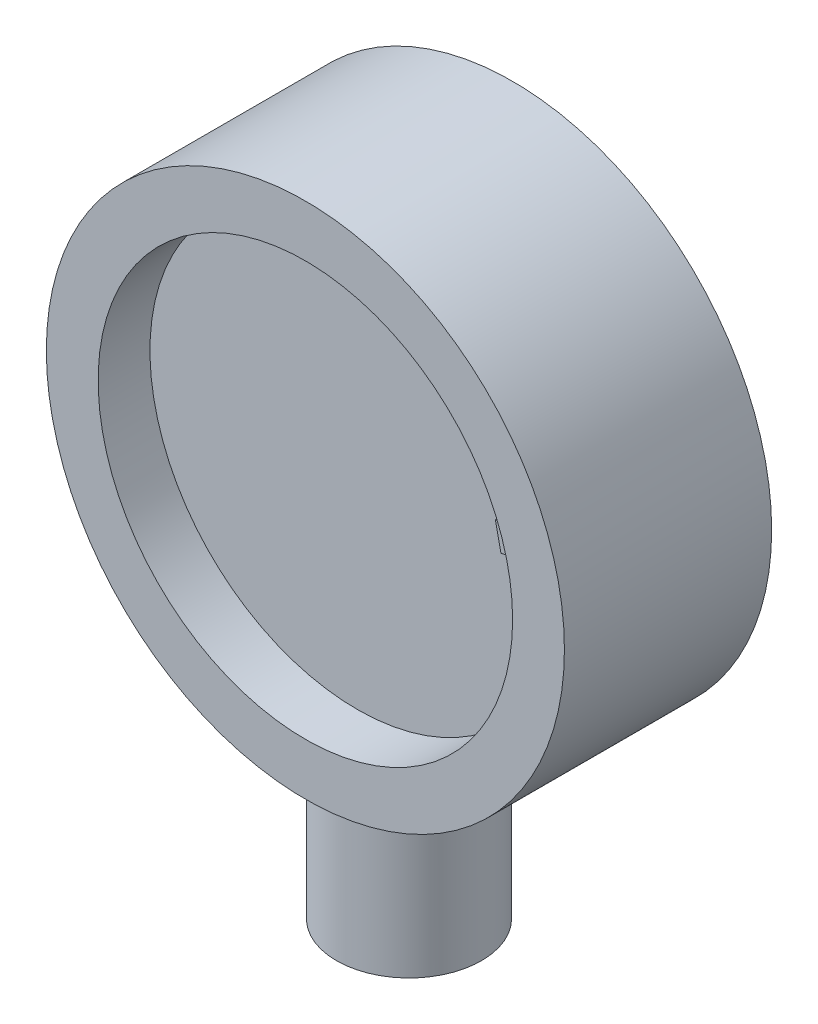
SolidWorks part; units mm, degrees
ref_plane "Спереди" through (0, 0, 0) normal (0, 0, 1) x (1, 0, 0)
ref_plane "Сверху" through (0, 0, 0) normal (0, 1, 0) x (1, 0, 0)
ref_plane "Справа" through (0, 0, 0) normal (1, 0, 0) x (0, 0, -1)
sketch "Эскиз1" plane through (0, 0, 0) normal (0, 0, 1) x (1, 0, 0)
  circle A0 centre (0, 0) radius 25
extrude "Бобышка-Вытянуть1" add sketch "Эскиз1" along normal blind 20
sketch "Эскиз2" plane through (0, 0, 0) normal (0, 1, 0) x (1, 0, 0)
  circle A0 centre (0, -10) radius 7
extrude "Бобышка-Вытянуть2" add sketch "Эскиз2" against normal blind 40
sketch "Эскиз3" plane through (0, 0, 20) normal (0, 0, 1) x (1, 0, 0)
  circle A0 centre (0, 0) radius 20
extrude "Вырез-Вытянуть1" cut sketch "Эскиз3" against normal blind 5
sketch "Эскиз4" plane through (0, 0, 15) normal (0, 0, 1) x (1, 0, 0)
  text T0 "кГс/см2"
extrude "Бобышка-Вытянуть3" add sketch "Эскиз4" along normal blind 2
